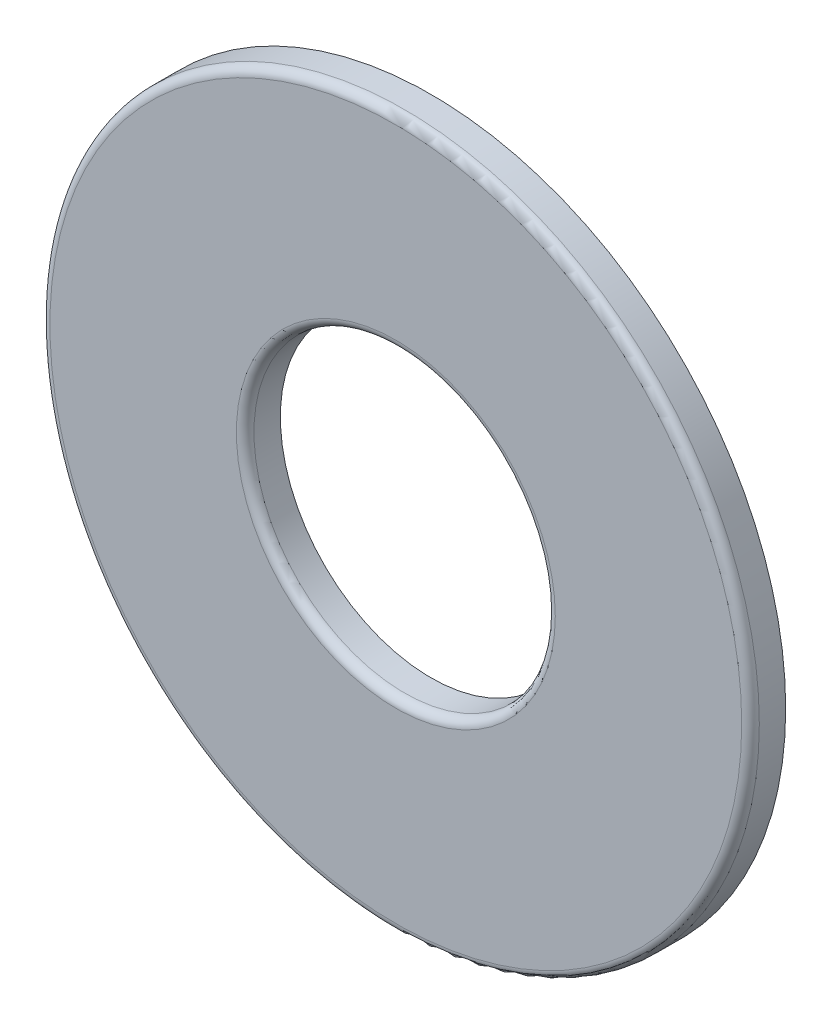
SolidWorks part; units mm, degrees
other "Imported1" parameters "D1"=0.3937, "TH"=1.0287, "Thickness"=1.5748
material "Plain Carbon Steel"
ref_plane "Front Plane" through (0, 0, 0) normal (0, 0, 1) x (1, 0, 0)
ref_plane "Top Plane" through (0, 0, 0) normal (0, 1, 0) x (1, 0, 0)
ref_plane "Right Plane" through (0, 0, 0) normal (1, 0, 0) x (0, 0, -1)
sketch "Sketch1" plane through (0, 0, 0) normal (0, 0, 1) x (1, 0, 0)
  line L0 (-15.875, 0) -> (15.875, 0) construction
  line L1 (-6.7437, 0) -> (6.7437, 0) construction
  circle A0 centre (0, 0) radius 6.7437 construction
  circle A1 centre (0, 0) radius 15.875 construction
  point P8 (0, 0)
  point P9 (0, 15.875)
  point P11 (6.7437, 0)
  dimension "ID" = 13.4874
  dimension "OD" = 31.75
sketch "Sketch2" plane through (0, 0, 0) normal (1, 0, 0) x (0, 0, -1)
  line L0 (-0.7874, 15.875) -> (0.7874, 15.875) construction
  point P2 (0, 15.875)
sketch "Sketch3" plane through (0, 0, 0) normal (0, 0, 1) x (1, 0, 0)
  circle A0 centre (0, 0) radius 6.7437
  circle A1 centre (0, 0) radius 15.875
extrude "Boss-Extrude1" add sketch "Sketch3" along normal up to vertex (0.7874 mm away) and the other way up to vertex (0.7874 mm away) up to point (0, 15.875, 0.7874) other way up to point (0, 15.875, -0.7874)
fillet "Fillet1" radius 0.3937 2 edges at (15.875, 0, 0.7874) (6.7437, 0, 0.7874)
equation "\"D1@Fillet1\"=\"Thickness@Sketch2\"/4"
